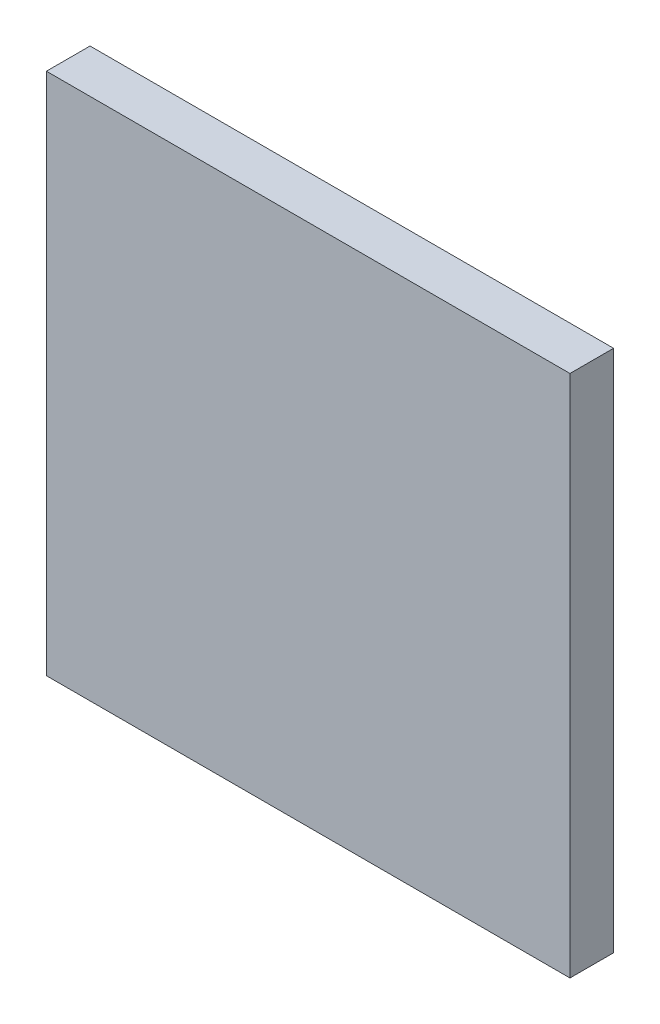
SolidWorks part; units mm, degrees
ref_plane "Front Plane" through (0, 0, 0) normal (0, 0, 1) x (1, 0, 0)
ref_plane "Top Plane" through (0, 0, 0) normal (0, 1, 0) x (1, 0, 0)
ref_plane "Right Plane" through (0, 0, 0) normal (1, 0, 0) x (0, 0, -1)
sketch "Sketch1" plane through (0, 0, 0) normal (0, 0, 1) x (1, 0, 0)
  line L1 (-19.05, 19.05) -> (19.05, 19.05)
  line L2 (-19.05, 19.05) -> (-19.05, -19.05)
  line L3 (-19.05, -19.05) -> (19.05, -19.05)
  line L4 (19.05, 19.05) -> (19.05, -19.05)
  line L5 (-19.05, 19.05) -> (19.05, -19.05) construction
  line L6 (-19.05, -19.05) -> (19.05, 19.05) construction
  point P0 (0, 0)
  dimension "D1" = 38.1
  dimension "D2" = 38.1
extrude "Boss-Extrude1" add sketch "Sketch1" along normal blind 3.175
sketch "Sketch2" plane through (0, 0, 3.175) normal (0, 0, 1) x (1, 0, 0)
  line L0 (19.05, 19.05) -> (-19.05, 19.05) construction
  line L1 (-19.05, 19.05) -> (-19.05, -19.05) construction
  circle A0 centre (-12.7, 12.7) radius 2.6287
  dimension "D1" = 6.35
  dimension "D2" = 5.2574
  dimension "D3" = 6.35
